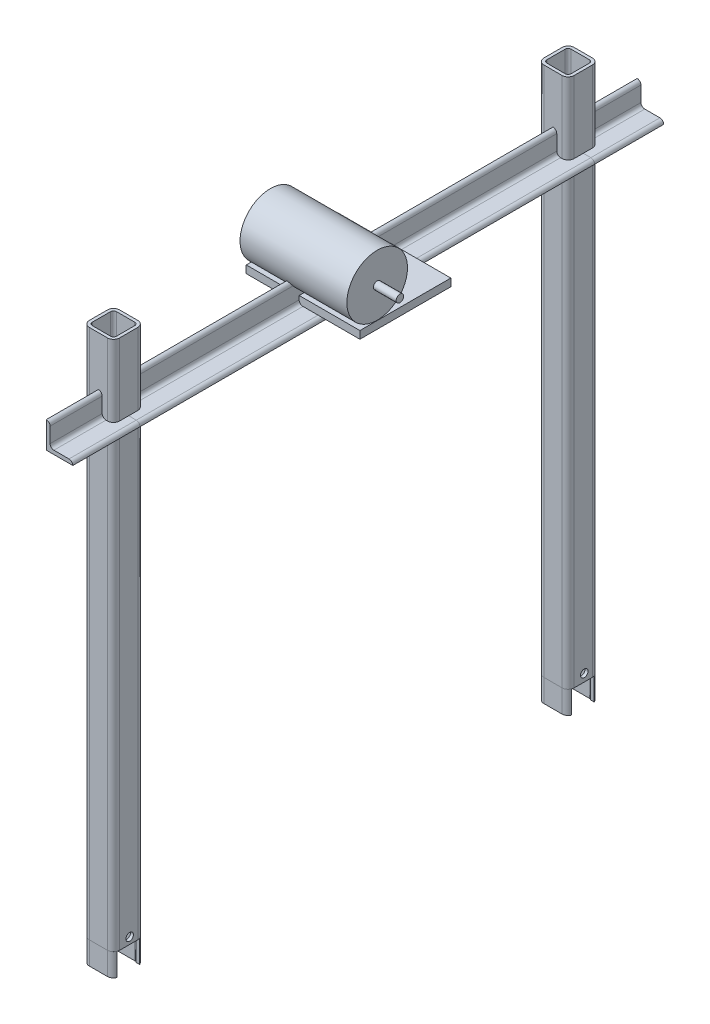
SolidWorks part; units mm, degrees
ref_plane "Front Plane" through (0, 0, 0) normal (0, 0, 1) x (1, 0, 0)
ref_plane "Top Plane" through (0, 0, 0) normal (0, 1, 0) x (1, 0, 0)
ref_plane "Right Plane" through (0, 0, 0) normal (1, 0, 0) x (0, 0, -1)
sketch "Sketch1" plane through (0, 0, 0) normal (1, 0, 0) x (0, 0, -1)
  line L0 (-53.2616, -661.0182) -> (-53.2616, 38.9818)
  line L1 (-53.2616, -661.0182) -> (-53.2616, -691.0182)
  line L2 (546.7384, 38.9818) -> (546.7384, -661.0182)
  line L3 (-53.2616, -61.0182) -> (546.7384, -61.0182)
  line L4 (546.7384, -661.0182) -> (546.7384, -691.0182)
  line L5 (546.7384, -61.0182) -> (637.868, -61.0182)
  line L6 (-53.2616, -61.0182) -> (-141.9908, -61.0182)
  dimension "D1" = 700
  dimension "D2" = 700
  dimension "D3" = 600
  dimension "D4" = 30
  dimension "D5" = 30
other "Structural Member1"
ref_plane "Plane1" through (0, -661.0182, 53.2616) normal (0, 1, 0) x (0, 0, 1)
sketch "Sketch11" plane through (0, -661.0182, 53.2616) normal (0, 1, 0) x (0, 0, 1)
  line L0 (-12, -16) -> (12, -16)
  line L1 (-16, -12) -> (-16, 12)
  line L2 (12, 16) -> (-12, 16)
  line L3 (16, 12) -> (16, -12)
  line L4 (-12, -20) -> (12, -20)
  line L5 (-20, -12) -> (-20, 12)
  line L6 (12, 20) -> (-12, 20)
  line L7 (20, 12) -> (20, -12)
  arc A0 (20, 12) -> (12, 20) centre (12, 12) ccw
  arc A1 (12, -20) -> (20, -12) centre (12, -12) ccw
  arc A2 (-20, -12) -> (-12, -20) centre (-12, -12) ccw
  arc A3 (-12, 20) -> (-20, 12) centre (-12, 12) ccw
  arc A4 (-12, 16) -> (-16, 12) centre (-12, 12) ccw
  arc A5 (16, 12) -> (12, 16) centre (12, 12) ccw
  arc A6 (12, -16) -> (16, -12) centre (12, -12) ccw
  arc A7 (-16, -12) -> (-12, -16) centre (-12, -12) ccw
  point P0 (-20, 0)
  point P1 (20, 0)
  point P2 (0, 20)
  point P3 (0, -20)
  point P4 (0, 0)
  point P5 (-20, -20)
  point P6 (20, -20)
  point P7 (20, 20)
  point P8 (-20, 20)
  point P33 (0, 0)
  dimension "D1" = 8
  dimension "Thickness" = 4
  dimension "V_leg" = 40
other "Structural Member3"
ref_plane "Plane3" through (0, -661.0182, 53.2616) normal (0, -1, 0) x (0, 0, -1)
sketch "Sketch13" plane through (0, -661.0182, 53.2616) normal (0, -1, 0) x (0, 0, -1)
  line L0 (-12, -16) -> (12, -16)
  line L1 (-16, -12) -> (-16, 12)
  line L2 (12, 16) -> (-12, 16)
  line L3 (16, 12) -> (16, -12)
  line L4 (-12, -20) -> (12, -20)
  line L5 (-20, -12) -> (-20, 12)
  line L6 (12, 20) -> (-12, 20)
  line L7 (20, 12) -> (20, -12)
  arc A0 (20, 12) -> (12, 20) centre (12, 12) ccw
  arc A1 (12, -20) -> (20, -12) centre (12, -12) ccw
  arc A2 (-20, -12) -> (-12, -20) centre (-12, -12) ccw
  arc A3 (-12, 20) -> (-20, 12) centre (-12, 12) ccw
  arc A4 (-12, 16) -> (-16, 12) centre (-12, 12) ccw
  arc A5 (16, 12) -> (12, 16) centre (12, 12) ccw
  arc A6 (12, -16) -> (16, -12) centre (12, -12) ccw
  arc A7 (-16, -12) -> (-12, -16) centre (-12, -12) ccw
  point P0 (-20, 0)
  point P1 (20, 0)
  point P2 (0, 20)
  point P3 (0, -20)
  point P4 (0, 0)
  point P5 (-20, -20)
  point P6 (20, -20)
  point P7 (20, 20)
  point P8 (-20, 20)
  point P33 (0, 0)
  dimension "D1" = 8
  dimension "Thickness" = 4
  dimension "V_leg" = 40
sketch "Sketch14" plane through (-20, 0, 0) normal (-1, 0, 0) x (0, 0, 1)
  line L0 (-534.7384, -691.0182) -> (-558.7384, -691.0182) construction
  line L1 (-561.7384, -691.0182) -> (-531.7384, -691.0182)
  line L2 (-561.7384, -691.0182) -> (-561.7384, -661.0182)
  line L3 (-561.7384, -661.0182) -> (-531.7384, -661.0182)
  line L4 (-531.7384, -691.0182) -> (-531.7384, -661.0182)
  line L5 (-534.7384, -661.0182) -> (-558.7384, -661.0182) construction
  line L6 (-558.7384, -691.0182) -> (-558.7384, -661.0182) construction
  dimension "D1" = 30
  dimension "D2" = 30
  dimension "D3" = 3
extrude "Cut-Extrude1" cut sketch "Sketch14" against normal blind 45
sketch "Sketch15" plane through (-20, 0, 0) normal (-1, 0, 0) x (0, 0, 1)
  line L0 (65.2616, -691.0182) -> (41.2616, -691.0182) construction
  line L1 (38.2616, -691.0182) -> (68.2616, -691.0182)
  line L2 (38.2616, -691.0182) -> (38.2616, -661.0182)
  line L3 (38.2616, -661.0182) -> (68.2616, -661.0182)
  line L4 (68.2616, -691.0182) -> (68.2616, -661.0182)
  line L5 (65.2616, -661.0182) -> (41.2616, -661.0182) construction
  line L6 (41.2616, -691.0182) -> (41.2616, -661.0182) construction
  dimension "D1" = 30
  dimension "D2" = 3
extrude "Cut-Extrude2" cut sketch "Sketch15" against normal blind 45
other "Structural Member4"
ref_plane "Plane8" through (0, -61.0182, 53.2616) normal (0, 0, -1) x (0, 1, 0)
sketch "Sketch110" plane through (0, -61.0182, 53.2616) normal (0, 0, -1) x (0, 1, 0)
  line L0 (0, 0) -> (0, 35)
  line L1 (0, 17.5) -> (5, 17.5) construction
  line L2 (5, 30) -> (5, 10)
  line L3 (10, 5) -> (30, 5)
  line L4 (17.5, 5) -> (17.5, 0) construction
  line L5 (35, 0) -> (0, 0)
  arc A0 (35, 0) -> (30, 5) centre (30, 0) ccw
  arc A1 (0, 35) -> (5, 30) centre (0, 30) cw
  arc A2 (10, 5) -> (5, 10) centre (10, 10) cw
  point P10 (17.5, 0)
  point P14 (0, 17.5)
  point P15 (5, 17.5)
  point P16 (17.5, 5)
  point P17 (5, 35)
  point P18 (35, 5)
  point P21 (0, 0)
  dimension "D2" = 5
  dimension "D3" = 35
  dimension "Radius_1" = 5
  dimension "D1" = 5
sketch "Sketch111" plane through (0, -56.0182, 0) normal (0, 1, 0) x (1, 0, 0)
  line L1 (30, 546.7384) -> (0, 546.7384)
  line L2 (85.1639, 186.7384) -> (-64.8361, 186.7384)
  line L3 (85.1639, 186.7384) -> (85.1639, 306.7384)
  line L4 (85.1639, 306.7384) -> (-64.8361, 306.7384)
  line L5 (-64.8361, 186.7384) -> (-64.8361, 306.7384)
  line L6 (30, 546.7384) -> (10, 546.7384) construction
  line L7 (10, 546.7384) -> (30, 546.7384) construction
  dimension "D1" = 120
  dimension "D2" = 150
  dimension "D3" = 240
extrude "Boss-Extrude1" add sketch "Sketch111" along normal blind 10 separate body contours L3 L4 L5 L2
sketch "Sketch112" plane through (85.1639, 0, 0) normal (1, 0, 0) x (0, 0, -1)
  circle A0 centre (209.5541, -5.6462) radius 40
  dimension "D1" = 80
extrude "Boss-Extrude2" add sketch "Sketch112" against normal blind 141 separate body
sketch "Sketch113" plane through (85.1639, 0, 0) normal (1, 0, 0) x (0, 0, -1)
  circle A0 centre (209.5541, -5.6462) radius 5
extrude "Boss-Extrude3" add sketch "Sketch113" along normal blind 30 separate body
sketch "Sketch114" plane through (20, 0, 0) normal (1, 0, 0) x (0, 0, -1)
  line L0 (534.7384, -661.0182) -> (558.7384, -661.0182) construction
  circle A0 centre (548.0405, -651.0182) radius 5
  circle A1 centre (-51.9595, -652.2443) radius 5
  dimension "D2" = 10
  dimension "D3" = 600
  dimension "D4" = 10
  dimension "D1" = 10
extrude "Cut-Extrude3" cut sketch "Sketch114" against normal blind 105
